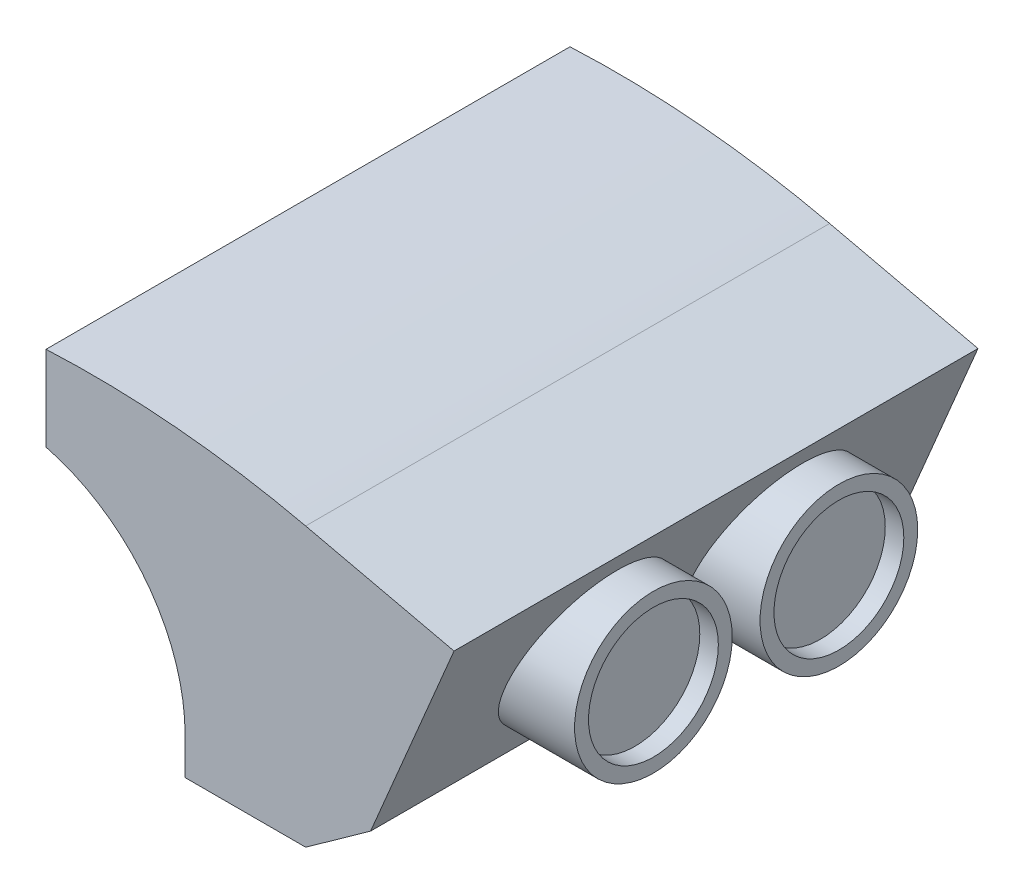
SolidWorks part; units mm, degrees
ref_plane "Front Plane" through (0, 0, 0) normal (0, 0, 1) x (1, 0, 0)
ref_plane "Top Plane" through (0, 0, 0) normal (0, 1, 0) x (1, 0, 0)
ref_plane "Right Plane" through (0, 0, 0) normal (1, 0, 0) x (0, 0, -1)
sketch "Sketch1" plane through (0, 0, 0) normal (0, 1, 0) x (1, 0, 0)
  line L0 (-14, 28.25) -> (14, 28.25)
  line L1 (14, 28.25) -> (14, -28.25)
  line L2 (-14, 28.25) -> (-14, -28.25)
  line L3 (-14, -28.25) -> (14, -28.25)
  point P6 (-14, 0)
  point P7 (0, 28.25)
  dimension "D1" = 56.5
  dimension "D2" = 28
extrude "Boss-Extrude1" add sketch "Sketch1" against normal blind 30 contours L0 L1 L3 L2
sketch "Sketch5" plane through (0, 0, -28.25) normal (0, 0, -1) x (-1, 0, 0)
  line L0 (-1, -30) -> (-1, -26)
  line L1 (14, -30) -> (-14, -30) construction
  line L2 (14, -30) -> (14, 0) construction
  line L3 (-1, -30) -> (14, -30)
  line L4 (14, -30) -> (14, -6.6351)
  arc A0 (-1, -26) -> (14, -6.6351) centre (19, -26) cw
  dimension "D1" = 20
  dimension "D2" = 4
  dimension "D3" = 15
extrude "Cut-Extrude2" cut sketch "Sketch5" against normal up to surface (56.5 mm away) contours A0 L4 L3 L0 up to face at (0, -15, 28.25)
shell "Shell1" thickness 1
ref_plane "Plane1" through (0, 0, -20) normal (0, 0, 1) x (1, 0, 0)
sketch "Sketch3" plane through (0, 0, -20) normal (0, 0, 1) x (1, 0, 0)
  line L0 (-14, -1) -> (-15, -1)
  line L1 (-14, -2) -> (-15, -2)
  line L2 (-14, -6.6351) -> (-14, 0) construction
  line L3 (-14, -2) -> (-12.5, -1)
  line L5 (-12.5, -1) -> (-14, -1)
  line L6 (-13, -1) -> (13, -1) construction
  line L7 (-14, -6.6351) -> (-14, 0) construction
  arc A0 (-15, -1) -> (-15, -2) centre (-15, -1.5) ccw
  dimension "D2" = 0.5
  dimension "D1" = 1
  dimension "D3" = 1.5
extrude "Boss-Extrude3" add sketch "Sketch3" along normal mid plane 5 contours A0 L1 L3 L5 L0
sketch "Sketch4" plane through (0, 0, -22.5) normal (0, 0, -1) x (-1, 0, 0)
  circle A0 centre (15, -1.5) radius 0.35
  arc A1 (15, -2) -> (15, -1) centre (15, -1.5) ccw construction
  dimension "D1" = 0.15
extrude "Cut-Extrude1" cut sketch "Sketch4" against normal up to surface (5 mm away) up to face at (-12.8333, -1.1111, -17.5)
mirror "Mirror1" about plane through (0, 0, 0) normal (0, 0, 1) of "Cut-Extrude1", "Boss-Extrude3"
sketch "Sketch6" plane through (0, 0, -28.25) normal (0, 0, -1) x (-1, 0, 0)
  line L0 (14, 0) -> (14, 2.5)
  line L1 (-14, 0) -> (-30, -3.6778)
  line L2 (-30, -3.6778) -> (-21, -25)
  line L3 (-21, -25) -> (-14, -30)
  line L4 (14, -6.6351) -> (14, 0) construction
  line L5 (14, 0) -> (-14, 0) construction
  line L6 (-14, -30) -> (-14, 0)
  line L7 (14, 0) -> (-14, 0)
  arc A0 (14, 2.5) -> (-14, 0) centre (9.0743, -100.3822) ccw
  line M3 (14, 0) -> (-14, 0)
  line M4 (-14, 0) -> (-14, -30)
  dimension "D2" = 103
  dimension "D1" = 2.5
  dimension "D3" = 35
  dimension "D4" = 44
  dimension "D5" = 25
extrude "Boss-Extrude4" add sketch "Sketch6" against normal up to surface (56.5 mm away) contours L2 L3 L1 M4 | L0 A0 M3 up to face at (0.8852, -15.0117, 28.25)
ref_plane "Plane2" through (33, 0, 0) normal (1, 0, 0) x (0, 0, -1)
sketch "Sketch7" plane through (33, 0, 0) normal (1, 0, 0) x (0, 0, -1)
  line L0 (-28.25, -3.6778) -> (-28.25, -25) construction
  line L1 (28.25, -3.6778) -> (28.25, -25) construction
  circle A0 centre (10.25, -14.3389) radius 8.5
  point P2 (-28.25, -14.3389)
  dimension "D2" = 17
  dimension "D1" = 18
extrude "Boss-Extrude5" add sketch "Sketch7" against normal up to surface (7.5 mm away)
sketch "Sketch8" plane through (33, 0, 0) normal (1, 0, 0) x (0, 0, -1)
  circle A0 centre (10.25, -14.3389) radius 7
  circle A1 centre (10.25, -14.3389) radius 8.5 construction
  dimension "D1" = 1.5
extrude "Cut-Extrude3" cut sketch "Sketch8" against normal blind 2
pattern_linear "LPattern1" count 2 spacing 20 along (0, 0, 1) of "Boss-Extrude5", "Cut-Extrude3"
